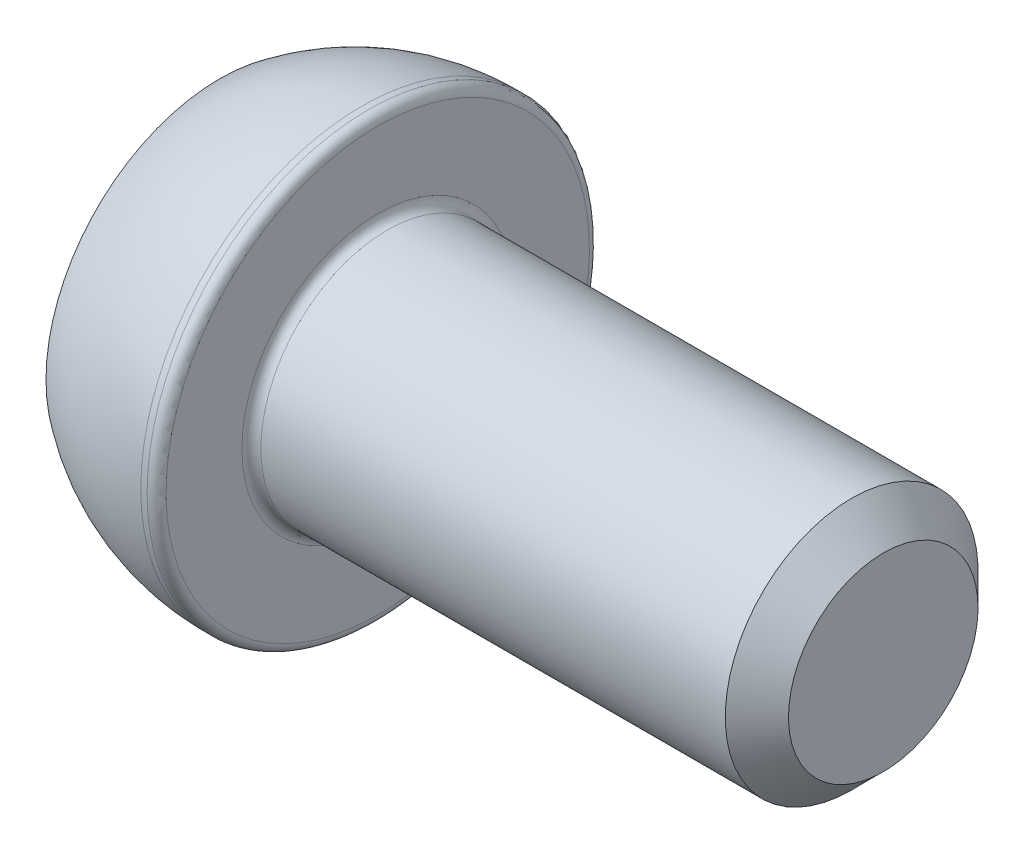
SolidWorks part; units mm, degrees
ref_plane "Спереди" through (0, 0, 0) normal (0, 0, 1) x (1, 0, 0)
ref_plane "Сверху" through (0, 0, 0) normal (0, 1, 0) x (1, 0, 0)
ref_plane "Справа" through (0, 0, 0) normal (1, 0, 0) x (0, 0, -1)
sketch "Эскиз1" plane through (0, 0, 0) normal (0, 0, 1) x (1, 0, 0)
  line L0 (0, 0) -> (0, 5.5)
  line L1 (4.5, 7) -> (5, 7)
  line L2 (5, 7) -> (5, 4)
  line L3 (5, 4) -> (21, 4)
  line L4 (21, 4) -> (21, 0)
  line L5 (21, 0) -> (0, 0) construction
  line L6 (0, 0) -> (21, 0)
  arc A0 (0, 5.5) -> (4.5, 7) centre (4.5, -0.5) cw
  point P9 (5, 5.5)
  dimension "D1" = 0.5
  dimension "D2" = 8
  dimension "D3" = 14
  dimension "D5" = 5
  dimension "D6" = 16
revolve "Повернуть1" add sketch "Эскиз1" angle 360 about L5
cosmetic thread "Условное изображение резьбы1" parameters "D2"=6.619
sketch "Эскиз2" plane through (0, 0, 0) normal (-1, 0, 0) x (0, 0, 1)
  line L1 (1.7321, 3) -> (-1.7321, 3)
  line L2 (-1.7321, 3) -> (-3.4641, 0)
  line L3 (-3.4641, 0) -> (-1.7321, -3)
  line L4 (-1.7321, -3) -> (1.7321, -3)
  line L5 (1.7321, -3) -> (3.4641, 0)
  line L6 (3.4641, 0) -> (1.7321, 3)
  circle A0 centre (0, 0) radius 3 construction
  dimension "D1" = 6
extrude "Вырез-Вытянуть1" cut sketch "Эскиз2" against normal blind 3
fillet "Скругление1" radius 0.3 2 edges at (5, 4, 0) (5, 7, 0)
chamfer "Фаска1" distance 1 angle 45 1 edges at (21, 4, 0)
